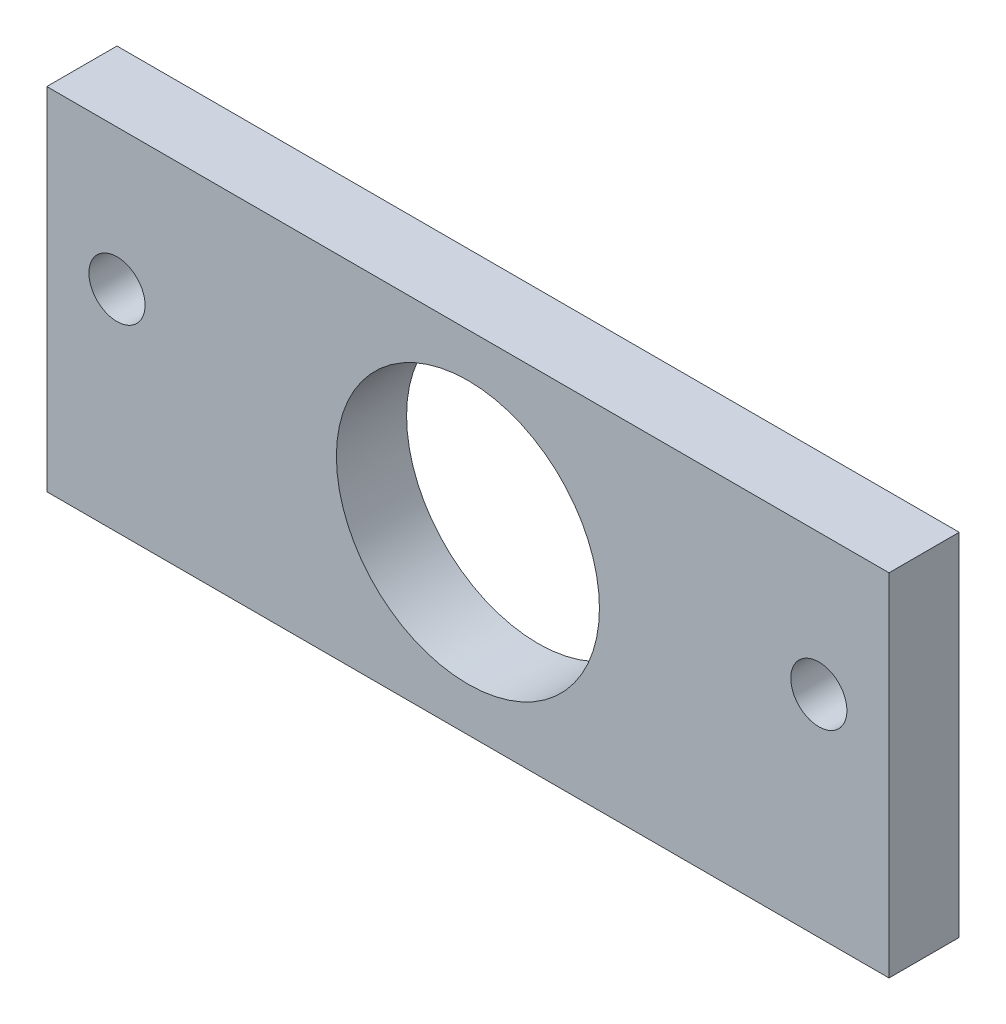
SolidWorks part; units mm, degrees
material "ABS"
ref_plane "Front Plane" through (0, 0, 0) normal (0, 0, 1) x (1, 0, 0)
ref_plane "Top Plane" through (0, 0, 0) normal (0, 1, 0) x (1, 0, 0)
ref_plane "Right Plane" through (0, 0, 0) normal (1, 0, 0) x (0, 0, -1)
sketch "Sketch1" plane through (0, 0, 0) normal (0, 0, 1) x (1, 0, 0)
  line L0 (0, 31.75) -> (76.2, 0) construction
  line L1 (0, 0) -> (76.2, 0)
  line L2 (0, 0) -> (0, 31.75)
  line L3 (0, 31.75) -> (76.2, 31.75)
  line L4 (76.2, 0) -> (76.2, 31.75)
  line L5 (0, 6.35) -> (18.8069, 6.35) construction
  line L12 (6.35, 6.35) -> (6.35, 31.75) construction
  line L14 (38.1, 31.75) -> (38.1, 0) construction
  circle A0 centre (38.1, 15.875) radius 11.8999
  circle A1 centre (6.35, 19.05) radius 2.54
  circle A2 centre (69.85, 19.05) radius 2.54
  point P5 (38.1, 15.875)
  point P23 (6.35, 19.05)
  dimension "D5" = 76.2
  dimension "D2" = 5.08
  dimension "D1" = 23.7998
  dimension "D3" = 31.75
  dimension "D4" = 6.35
  dimension "D6" = 6.35
extrude "Boss-Extrude1" add sketch "Sketch1" along normal blind 6.35
equation "\"base length\"= 21"
equation "\"glass pane length\"= 14.125"
equation "\"glass pane width\"= 10.1875"
equation "\"glass pane wall width\"= 3/4"
equation "\"glass lip\"= 1/4"
equation "\"bolt diameter\"= 0.2"
equation "\"stepper body width\"= 2.22"
equation "\"stepper mount offset\"= 0.19"
equation "\"stepper mount diameter\"= 0.19"
equation "\"stepper shaft offset from body\"= 0.79"
equation "\"stepper spacer thickness\"= 0.2"
equation "\"y axis stepper wall height off base\"= 8"
equation "\"y axis stepper wall bracket thickness\"= 1"
equation "\"y axis stepper wall mount side offset\"= 1/2"
equation "\"y axis stepper wall mount top offset\"= 1/2"
equation "\"y axis stepper wall width\"= \"stepper body width\" + 1                  "
equation "\"thin metal\"= 0.12"
equation "\"thick metal\"= 0.25"
equation "\"foot diameter\"= 0.2"
equation "\"foot inset from corner\"= 1"
equation "\"D1@Boss-Extrude1\" = \"thick metal\""
equation "\"recognizer width\"= 2.5"
equation "\"recognizer nut plate height\"= 1.25"
equation "\"recognizer nut plate offset\"= 1.5"
equation "\"D2@Sketch1\"=\"bolt diameter\""
equation "\"D3@Sketch1\"=\"recognizer nut plate height\""
equation "\"D6@Sketch1\"=0.5/2"
equation "\"D4@Sketch1\"=\"thick metal\""
